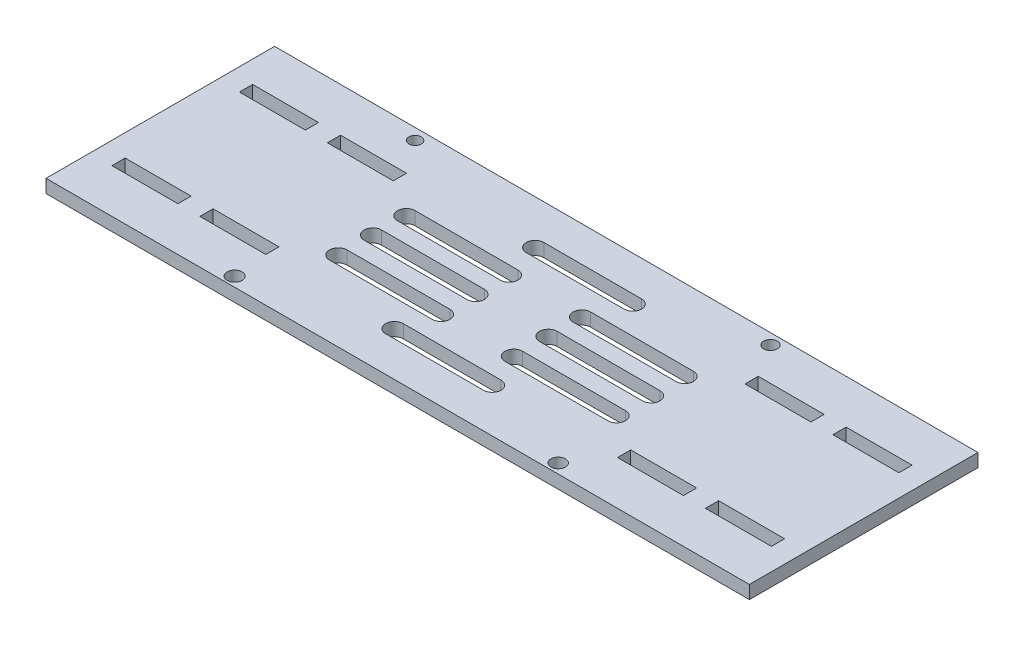
SolidWorks part; units mm, degrees
ref_plane "Front Plane" through (0, 0, 0) normal (0, 0, 1) x (1, 0, 0)
ref_plane "Top Plane" through (0, 0, 0) normal (0, 1, 0) x (1, 0, 0)
ref_plane "Right Plane" through (0, 0, 0) normal (1, 0, 0) x (0, 0, -1)
sketch "Sketch1" plane through (0, 0, 0) normal (0, 1, 0) x (1, 0, 0)
  line L0 (0, 0) -> (-15.3333, 0) construction
  line L1 (80, 26) -> (-80, 26)
  line L2 (80, 26) -> (80, -26)
  line L3 (80, -26) -> (-80, -26)
  line L4 (-80, 26) -> (-80, -26)
  line L6 (75, 16) -> (60, 16)
  line L7 (75, 16) -> (75, 13)
  line L8 (75, 13) -> (60, 13)
  line L9 (60, 16) -> (60, 13)
  line L10 (55, 16) -> (40, 16)
  line L11 (55, 16) -> (55, 13)
  line L12 (55, 13) -> (40, 13)
  line L13 (40, 16) -> (40, 13)
  line L15 (0, 0) -> (0, -4.375) construction
  line L19 (60, -16) -> (60, -13)
  line L20 (75, -13) -> (60, -13)
  line L21 (75, -16) -> (75, -13)
  line L22 (75, -16) -> (60, -16)
  line L23 (40, -16) -> (40, -13)
  line L24 (55, -13) -> (40, -13)
  line L25 (55, -16) -> (55, -13)
  line L26 (55, -16) -> (40, -16)
  line L28 (-55, -16) -> (-40, -16)
  line L29 (-55, -16) -> (-55, -13)
  line L30 (-55, -13) -> (-40, -13)
  line L31 (-40, -16) -> (-40, -13)
  line L32 (-75, -16) -> (-60, -16)
  line L33 (-75, -16) -> (-75, -13)
  line L34 (-75, -13) -> (-60, -13)
  line L35 (-60, -16) -> (-60, -13)
  line L40 (-40, 16) -> (-40, 13)
  line L41 (-55, 13) -> (-40, 13)
  line L42 (-55, 16) -> (-55, 13)
  line L43 (-55, 16) -> (-40, 16)
  line L44 (-60, 16) -> (-60, 13)
  line L45 (-75, 13) -> (-60, 13)
  line L46 (-75, 16) -> (-75, 13)
  line L47 (-75, 16) -> (-60, 16)
  dimension "D1" = 3
  dimension "D2" = 15
  dimension "D3" = 5
  dimension "D4" = 5
  dimension "D5" = 15
  dimension "D6" = 13
  dimension "D7" = 52
  dimension "D8" = 26
  dimension "D11" = 80
extrude "Boss-Extrude1" add sketch "Sketch1" along normal blind 3
sketch "Sketch2" plane through (0, 3, 0) normal (0, 1, 0) x (1, 0, 0)
  line L0 (-31.6585, 2) -> (-8.2664, 2)
  line L1 (31.6585, -9.8567) -> (8.2664, -9.8567)
  line L2 (31.6585, -5.8567) -> (8.2664, -5.8567)
  line L3 (-10.7477, 17.9876) -> (11.4995, 17.9876)
  line L4 (-31.6585, -2) -> (-8.2664, -2)
  line L5 (-31.6585, 9.6208) -> (-8.2664, 9.6208)
  line L6 (-31.6585, 5.6208) -> (-8.2664, 5.6208)
  line L7 (31.6585, 5.6208) -> (8.2664, 5.6208)
  line L8 (31.6585, 9.6208) -> (8.2664, 9.6208)
  line L9 (-31.6585, -5.8567) -> (-8.2664, -5.8567)
  line L10 (31.6585, -2) -> (8.2664, -2)
  line L11 (31.6585, 2) -> (8.2664, 2)
  line L12 (-31.6585, -9.8567) -> (-8.2664, -9.8567)
  line L13 (-10.7477, -13.9876) -> (11.4995, -13.9876)
  line L14 (-10.7477, -17.9876) -> (11.4995, -17.9876)
  line L15 (0, 0) -> (-4.1634, 0) construction
  line L16 (-10.7477, 13.9876) -> (11.4995, 13.9876)
  arc A0 (31.6585, -9.8567) -> (31.6585, -5.8567) centre (31.6585, -7.8567) ccw
  arc A1 (8.2664, -5.8567) -> (8.2664, -9.8567) centre (8.2664, -7.8567) ccw
  arc A2 (-8.2664, 2) -> (-8.2664, -2) centre (-8.2664, 0) cw
  arc A3 (-31.6585, -2) -> (-31.6585, 2) centre (-31.6585, 0) cw
  arc A4 (31.6585, 5.6208) -> (31.6585, 9.6208) centre (31.6585, 7.6208) ccw
  arc A5 (8.2664, 9.6208) -> (8.2664, 5.6208) centre (8.2664, 7.6208) ccw
  arc A6 (31.6585, -2) -> (31.6585, 2) centre (31.6585, 0) ccw
  arc A7 (8.2664, 2) -> (8.2664, -2) centre (8.2664, 0) ccw
  arc A8 (-8.2664, 9.6208) -> (-8.2664, 5.6208) centre (-8.2664, 7.6208) cw
  arc A9 (-31.6585, 5.6208) -> (-31.6585, 9.6208) centre (-31.6585, 7.6208) cw
  arc A10 (-8.2664, -5.8567) -> (-8.2664, -9.8567) centre (-8.2664, -7.8567) cw
  arc A11 (-31.6585, -9.8567) -> (-31.6585, -5.8567) centre (-31.6585, -7.8567) cw
  arc A12 (-10.7477, -13.9876) -> (-10.7477, -17.9876) centre (-10.7477, -15.9876) ccw
  arc A13 (11.4995, -17.9876) -> (11.4995, -13.9876) centre (11.4995, -15.9876) ccw
  arc A14 (11.4995, 17.9876) -> (11.4995, 13.9876) centre (11.4995, 15.9876) cw
  arc A15 (-10.7477, 13.9876) -> (-10.7477, 17.9876) centre (-10.7477, 15.9876) cw
  dimension "D1" = 4
extrude "Cut-Extrude1" cut sketch "Sketch2" against normal blind 3
sketch "Sketch3" plane through (0, 3, 0) normal (0, 1, 0) x (1, 0, 0)
  circle A0 centre (34.3231, -23.8155) radius 1.6358
  circle A1 centre (-39.2763, -23.8155) radius 1.6925
  circle A2 centre (-45.4844, 23.4378) radius 1.4101
  circle A3 centre (35.2358, 23.5655) radius 1.5508
extrude "Cut-Extrude2" cut sketch "Sketch3" against normal blind 10
